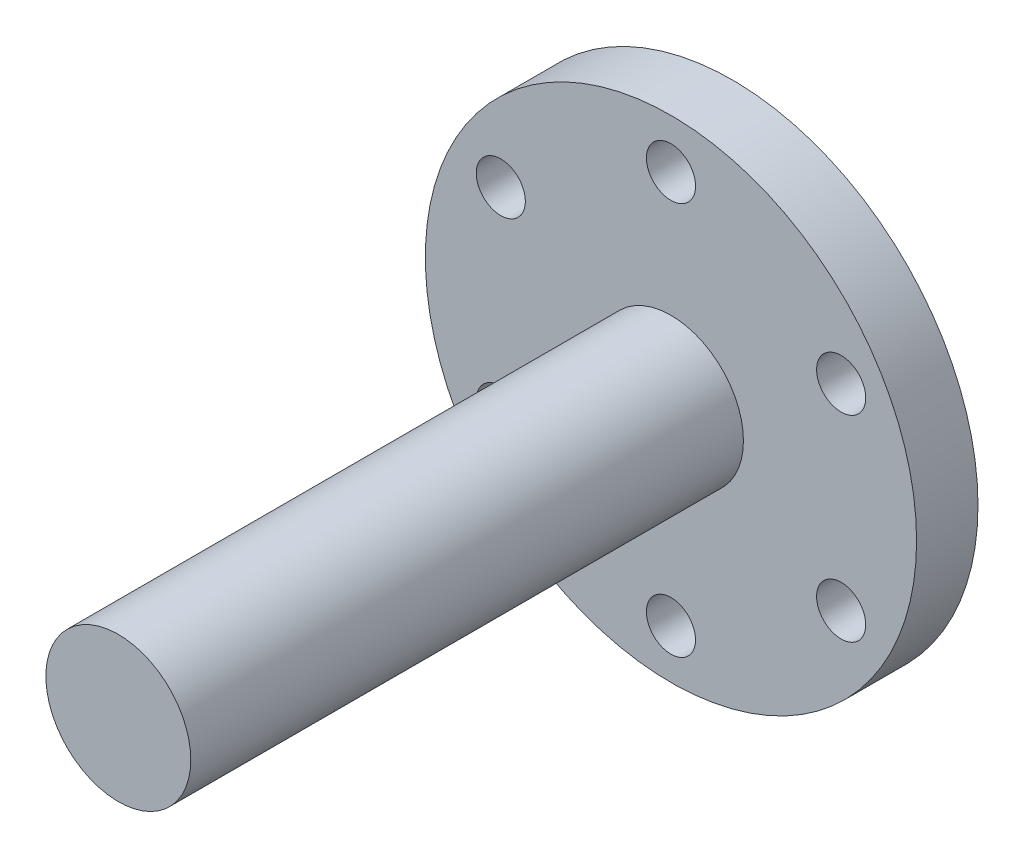
SolidWorks part; units mm, degrees
ref_plane "Front Plane" through (0, 0, 0) normal (0, 0, 1) x (1, 0, 0)
ref_plane "Top Plane" through (0, 0, 0) normal (0, 1, 0) x (1, 0, 0)
ref_plane "Right Plane" through (0, 0, 0) normal (1, 0, 0) x (0, 0, -1)
sketch "Sketch1" plane through (0, 0, 0) normal (0, 0, 1) x (1, 0, 0)
  circle A0 centre (0, 0) radius 20
  dimension "D1" = 40
extrude "Boss-Extrude1" add sketch "Sketch1" along normal blind 5
sketch "Sketch2" plane through (0, 0, 5) normal (0, 0, 1) x (1, 0, 0)
  circle A0 centre (0, 0) radius 5.9
  dimension "D1" = 11.8
extrude "Boss-Extrude2" add sketch "Sketch2" along normal blind 45
sketch "Sketch3" plane through (0, 0, 5) normal (0, 0, 1) x (1, 0, 0)
  circle A0 centre (0, 0) radius 16 construction
  circle A1 centre (0, 16) radius 2
  circle A2 centre (13.8564, 8) radius 2
  circle A3 centre (13.8564, -8) radius 2
  circle A4 centre (0, -16) radius 2
  circle A5 centre (-13.8564, -8) radius 2
  circle A6 centre (-13.8564, 8) radius 2
  point P18 (0, 0)
  dimension "D1" = 32
  dimension "D2" = 4
  dimension "D3" = 6
extrude "Cut-Extrude1" cut sketch "Sketch3" against normal blind 5
